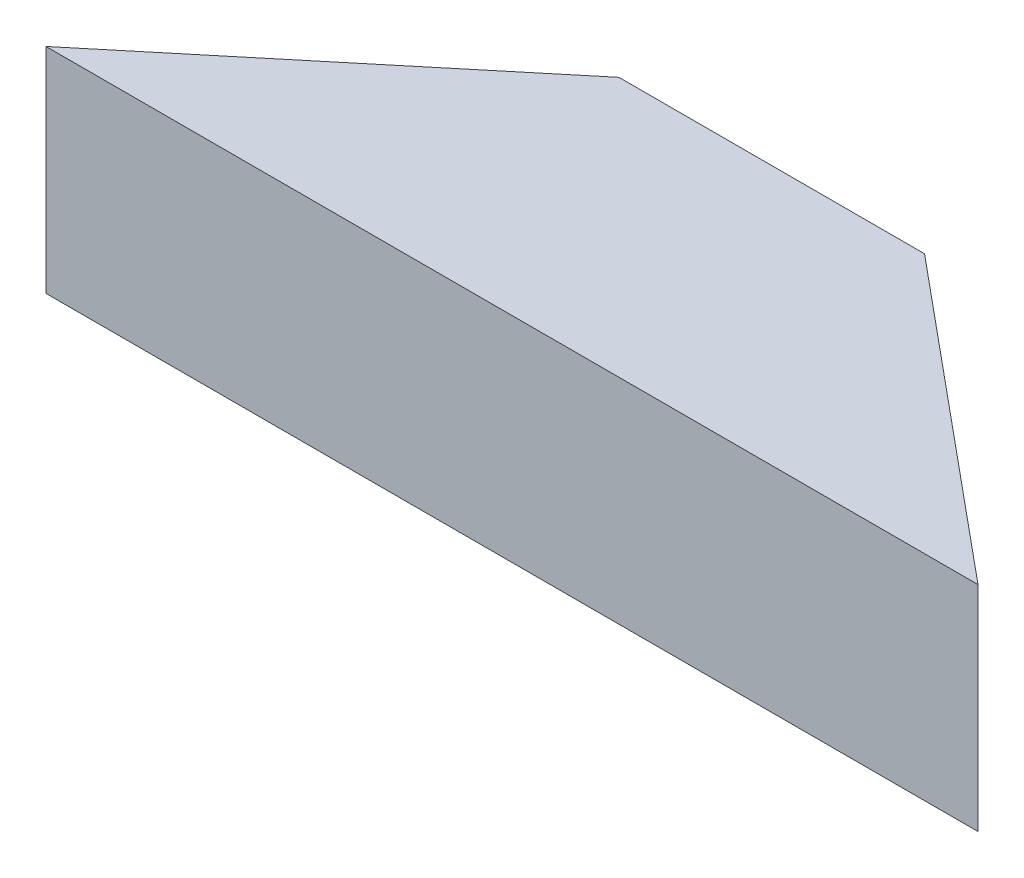
SolidWorks part; units mm, degrees
ref_plane "Plan de face" through (0, 0, 0) normal (0, 0, 1) x (1, 0, 0)
ref_plane "Plan de dessus" through (0, 0, 0) normal (0, 1, 0) x (1, 0, 0)
ref_plane "Plan de droite" through (0, 0, 0) normal (1, 0, 0) x (0, 0, -1)
sketch "Esquisse1" plane through (0, 0, 0) normal (0, 1, 0) x (1, 0, 0)
  line L0 (0, 0) -> (12.2, 0)
  line L1 (12.2, 0) -> (8.1, 3.4)
  line L2 (8.1, 3.4) -> (4.1, 3.4)
  line L3 (4.1, 3.4) -> (0, 0)
  line L4 (6.1, 0) -> (6.1, 11.518) construction
  dimension "D1" = 12.2
  dimension "D2" = 4
  dimension "D3" = 2
  dimension "D4" = 3.4
extrude "Boss.-Extru.1" add sketch "Esquisse1" along normal blind 2.8
